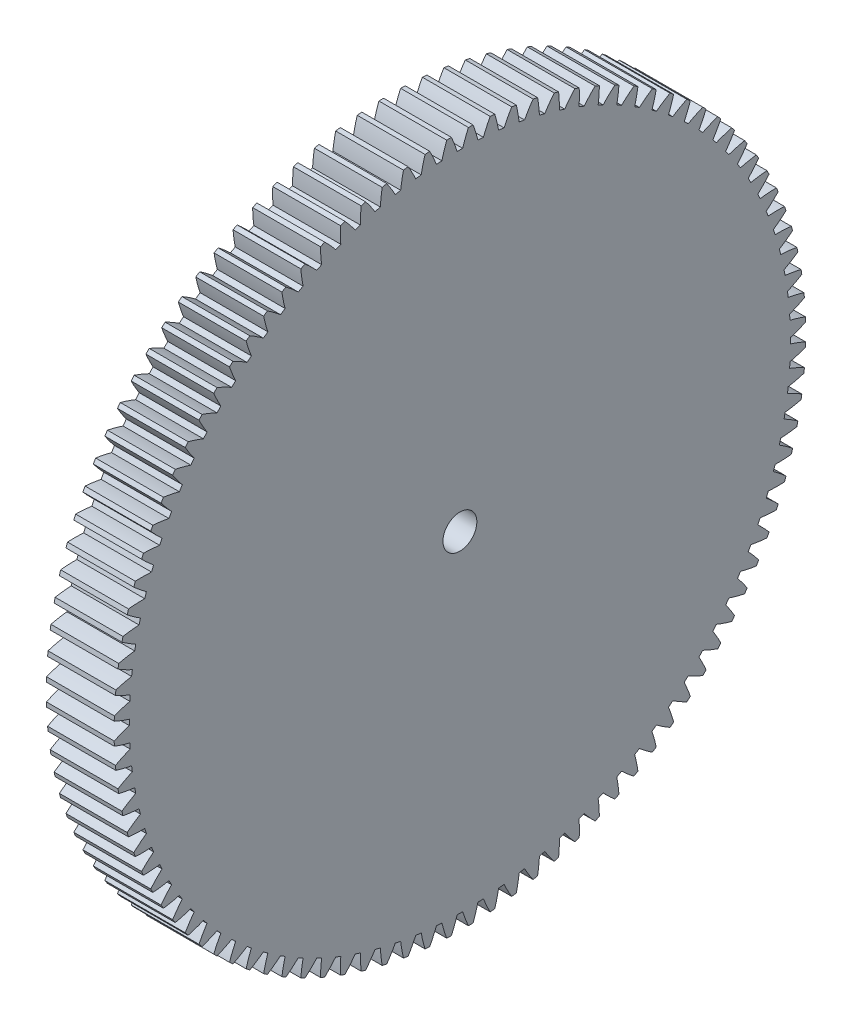
SolidWorks part; units mm, degrees
ref_plane "Plane1" through (0, 0, 0) normal (0, 0, 1) x (1, 0, 0)
ref_plane "Plane2" through (0, 0, 0) normal (0, 1, 0) x (1, 0, 0)
ref_plane "Plane3" through (0, 0, 0) normal (1, 0, 0) x (0, 0, -1)
sketch "HoldingSke" plane through (0, 0, 0) normal (0, 1, 0) x (1, 0, 0)
  line L0 (0, 0) -> (-0.0868, -0.4924)
  line L1 (-15, 0) -> (100, 0) construction
  line L2 (0, 0) -> (-2.1039, 2.3779)
  line L3 (0, 0) -> (-11.863, 4.5341)
  line L4 (0, 0) -> (-1.4996, 8.5048)
  line L5 (0, 0) -> (-46.8476, -17.4728)
  line L6 (0, 0) -> (-16.5793, -11.1861)
  line L7 (-2.1039, 2.3779) -> (8.6586, 51.2059)
  line L8 (-76.2, 54.61) -> (-74.4, 54.61)
  line L9 (-71.009, 38.7566) -> (-53.1078, 45.2721)
  line L10 (-76.2, 71.12) -> (104.1128, 71.12)
  line L11 (0, 0) -> (-20, 0)
  line L12 (-76.2, 101.6) -> (-76.133, 101.6)
  line L13 (24.9733, 27.94) -> (52.9518, 28.4284)
  line L14 (24.9733, 27.94) -> (24.9743, 27.94)
  line L15 (24.9733, 27.94) -> (100.4006, 29.5858)
  line L16 (-63.627, -2) -> (-12.827, -2)
  circle A0 centre (0, 0) radius 5
  circle A1 centre (0, 0) radius 37.5
  circle A2 centre (0, 0) radius 37.5
  circle A3 centre (0, 0) radius 5
  dimension "MHD" = 75
  dimension "Hub_dia" = 75
  dimension "Bore" = 10
  dimension "MBD" = 10
  dimension "Num_teeth" = 100
  dimension "Pitch" = 0.5
  dimension "Overall_len" = 50
  dimension "Show_teeth" = 100
  dimension "Thickness" = 20
  dimension "OAL" = 50.0001
  dimension "T_dim" = 1.8
  dimension "Ap" = 20
  dimension "H" = 19.05
  dimension "Pitch_radius" = 180.3128
  dimension "Width" = 20
  dimension "Backlash" = 0.067
  dimension "Addendum_fac" = 1
  dimension "Dedendum_fac" = 1.25
  dimension "Clearance_fac" = 0.25
  dimension "Dedendum_add" = 0.001
  dimension "Module" = 2
sketch "BasProSke" plane through (0, 0, 0) normal (0, 1, 0) x (1, 0, 0)
  line L0 (-10, 0) -> (60, 0) construction
  line L1 (0, 0) -> (0, 102)
  line L2 (0, 0) -> (20, 0)
  line L3 (20, 0) -> (20, 102)
  line L4 (20, 102) -> (0, 102)
  dimension "Thickness" = 20
  dimension "Diameter" = 204
revolve "Base-Revolve" add sketch "BasProSke" angle 360 about L0
sketch "TooCutSke" plane through (0, 0, 0) normal (1, 0, 0) x (0, 0, -1)
  line L1 (0, 0) -> (0, 107) construction
  line L2 (0, 0) -> (-1.688, 99.9858) construction
  line L3 (0, 0) -> (-6.2815, 199.8802) construction
  line L4 (-1.688, 99.9858) -> (-3.1407, 99.9401) construction
  arc A0 (0.8143, 97.4956) -> (-0.8143, 97.4956) centre (0, 0) ccw
  arc A1 (2.5315, 101.994) -> (-2.5315, 101.994) centre (0, 0) ccw
  circle A2 centre (0, 0) radius 100 construction
  circle A3 centre (0, 0) radius 93.9693 construction
  arc A4 (-0.8143, 97.4956) -> (-2.5315, 101.994) centre (-38.975, 85.5054) ccw
  arc A5 (2.5315, 101.994) -> (0.8143, 97.4956) centre (38.975, 85.5054) ccw
  dimension "Root_dia" = 194.998
  dimension "Overcut_dia" = 204.0508
  dimension "Pitch_dia" = 200
  dimension "Base_dia" = 187.9385
  dimension "Flank_rad" = 40
  dimension "Half_ang" = 1.8
  dimension "Half_CT" = 1.4535
extrude "ToothCut" cut sketch "TooCutSke" along normal through all
fillet "Breaks" [suppressed] radius 0.04
fillet "RootFillets" [suppressed] radius 0.501
pattern_circular "TeethCuts" count 100 every 3.6 about axis through (-10, 0, 0) along (1, 0, 0) of "ToothCut", "RootFillets", "Breaks"
sketch "HubNeaOneSke" plane through (0, 0, 0) normal (-1, 0, 0) x (0, 0, 1)
  circle A0 centre (0, 0) radius 37.5
  dimension "Diameter" = 75
extrude "HubNearOne" [suppressed] add sketch "HubNeaOneSke" along normal blind 30.0001
sketch "HubNeaBotSke" plane through (0, 0, 0) normal (-1, 0, 0) x (0, 0, 1)
  circle A0 centre (0, 0) radius 37.5
  dimension "Diameter" = 75
extrude "HubNearBoth" [suppressed] add sketch "HubNeaBotSke" along normal blind 15
ref_plane "FarPln" through (20, 0, 0) normal (1, 0, 0) x (0, 0, -1)
sketch "HubFarSke" plane through (20, 0, 0) normal (1, 0, 0) x (0, 0, -1)
  circle A0 centre (0, 0) radius 37.5
  dimension "Diameter" = 75
extrude "HubFar" [suppressed] add sketch "HubFarSke" along normal blind 15
sketch "BorSke" plane through (0, 0, 0) normal (1, 0, 0) x (0, 0, -1)
  circle A0 centre (0, 0) radius 5
  dimension "Diameter" = 10
extrude "Bore" cut sketch "BorSke" along normal mid plane 100.0001
sketch "KeySke" plane through (0, 0, 0) normal (1, 0, 0) x (0, 0, -1)
  line L0 (-2, 0) -> (-2, 6.8)
  line L1 (-2, 6.8) -> (2, 6.8)
  line L2 (2, 6.8) -> (2, 0)
  line L3 (0, 0) -> (0, 34) construction
  line L4 (-2, 0) -> (2, 0)
  dimension "Offset" = 6.8
  dimension "Width" = 4
extrude "Keyway" [suppressed] cut sketch "KeySke" along normal mid plane 100.0001
pattern_circular "Keyway2" [suppressed] count 2 every 90 about axis through (-10, 0, 0) along (1, 0, 0)
equation "' \"Module@HoldingSke\" = 6.35"
equation "' \"Num_teeth@HoldingSke\" = 12"
equation "' \"Ap@HoldingSke\" =  20"
equation "' \"Ap@HoldingSke\" = 20"
equation "' \"Width@HoldingSke\" = 0.5 * 25.4"
equation "' \"Hub_dia@HoldingSke\"= 1 * 25.4"
equation "' \"Hub_dia@HoldingSke\" = 1 * 25.4"
equation "' \"Overall_len@HoldingSke\" = 1.0 * 25.4"
equation "' \"Bore@HoldingSke\" = 0.75 * 25.4"
equation "' \"T_dim@HoldingSke\" = 0.1 * 25.4"
equation "' \"Width@KeySke\" = 0.25 * 25.4"
equation "' \"Show_teeth@HoldingSke\" = 13"
equation "' \"Backlash@HoldingSke\" = 0.009 * 25.4"
equation "' \"Addendum_fac@HoldingSke\" = 1.0"
equation "' \"Dedendum_fac@HoldingSke\" = 1.25"
equation "' \"Dedendum_add@HoldingSke\" = 0.00005 * 25.4"
equation "' \"Clearance_fac@HoldingSke\" = 0.25"
equation "\"Pitch@HoldingSke\" = 1 / \"Module@HoldingSke\""
equation "\"Overcut_dia@TooCutSke\" = (\"Num_teeth@HoldingSke\" + 2 * \"Addendum_fac@HoldingSke\") / \"Pitch@HoldingSke\" + 0.002 * 25.4"
equation "\"Pitch_dia@TooCutSke\" = \"Num_teeth@HoldingSke\" / \"Pitch@HoldingSke\""
equation "\"Base_dia@TooCutSke\" = \"Num_teeth@HoldingSke\" / \"Pitch@HoldingSke\" * cos((\"Ap@HoldingSke\"  * 3.14159265 / 180))"
equation "\"Root_dia@TooCutSke\" = (\"Num_teeth@HoldingSke\" + 2) / \"Pitch@HoldingSke\" - 2 * (\"Addendum_fac@HoldingSke\" + \"Dedendum_fac@HoldingSke\") / \"Pitch@HoldingSke\" - \"Dedendum_add@HoldingSke\" * 2"
equation "\"Half_ang@TooCutSke\" = 180 / \"Num_teeth@HoldingSke\""
equation "\"Half_CT@TooCutSke\" = \"Num_teeth@HoldingSke\" / \"Pitch@HoldingSke\" * sin((3.14159265 / 2 / \"Num_teeth@HoldingSke\")) / 2 - 7 * \"Backlash@HoldingSke\" / 4"
equation "\"Flank_rad@TooCutSke\" = \"Num_teeth@HoldingSke\" / \"Pitch@HoldingSke\" / 5"
equation "\"Radius@RootFillets\" = \"Clearance_fac@HoldingSke\" / \"Pitch@HoldingSke\" + \"Dedendum_add@HoldingSke\""
equation "\"Break_rad@Breaks\" = 0.02 / \"Pitch@HoldingSke\""
equation "\"Thickness@HoldingSke\" = \"Width@HoldingSke\""
equation "\"OAL@HoldingSke\" = \"Thickness@HoldingSke\""
equation "\"MHD@HoldingSke\" = (\"Num_teeth@HoldingSke\" + 2) / \"Pitch@HoldingSke\" - 2 * (\"Addendum_fac@HoldingSke\" + \"Dedendum_fac@HoldingSke\")  / \"Pitch@HoldingSke\" - \"Dedendum_add@HoldingSke\" * 2"
equation "\"MBD@HoldingSke\" = (\"Num_teeth@HoldingSke\" + 2) / \"Pitch@HoldingSke\" - 2 * (\"Addendum_fac@HoldingSke\" + \"Dedendum_fac@HoldingSke\")  / \"Pitch@HoldingSke\" - \"Dedendum_add@HoldingSke\" * 2 - 0.002 * 25.4"
equation "\"MHD@HoldingSke\" = ((sgn( \"MHD@HoldingSke\" - \"Hub_dia@HoldingSke\" )-1)*( \"MHD@HoldingSke\" - \"Hub_dia@HoldingSke\" ))/-2+ \"Hub_dia@HoldingSke\""
equation "\"MBD@HoldingSke\" = ((sgn( \"MBD@HoldingSke\" - \"Bore@HoldingSke\" )-1)*( \"MBD@HoldingSke\" - \"Bore@HoldingSke\" ))/-2+ \"Bore@HoldingSke\""
equation "\"OAL@HoldingSke\" = ((sgn( \"OAL@HoldingSke\" - \"Overall_len@HoldingSke\" )+1)*( \"OAL@HoldingSke\" - \"Overall_len@HoldingSke\" ))/2 + \"Overall_len@HoldingSke\" + 0.000002 * 25.4"
equation "\"Num_teeth@TeethCuts\" = int( \"Show_teeth@HoldingSke\" ) + 1"
equation "\"Num_teeth@TeethCuts\" = ((sgn( \"Num_teeth@TeethCuts\" - \"Num_teeth@HoldingSke\" )-1)*( \"Num_teeth@TeethCuts\" - \"Num_teeth@HoldingSke\" ))/-2+ \"Num_teeth@HoldingSke\""
equation "\"Num_teeth@TeethCuts\" = ((sgn( \"Num_teeth@TeethCuts\" - 2.0)+1)*( \"Num_teeth@TeethCuts\" - 2.0))/2 +2.0"
equation "\"Angle@TeethCuts\" = 360.0 / \"Num_teeth@HoldingSke\""
equation "\"Diameter@BasProSke\" = (\"Num_teeth@HoldingSke\" + 2 * \"Addendum_fac@HoldingSke\") / \"Pitch@HoldingSke\""
equation "\"Thickness@BasProSke\"  = \"Thickness@HoldingSke\""
equation "' \"Fillet_rad@BasProSke\" =  \"Thickness@HoldingSke\" * 0.05"
equation "' \"Fillet_rad@BasProSke\" = \"Thickness@HoldingSke\" * 0.05"
equation "\"MHD@HoldingSke\" = ((sgn( \"MHD@HoldingSke\" - \"Root_dia@TooCutSke\" )-1)*( \"MHD@HoldingSke\" - \"Root_dia@TooCutSke\" ))/-2+ \"Root_dia@TooCutSke\""
equation "\"Diameter@HubNeaOneSke\" = \"MHD@HoldingSke\""
equation "\"Length@HubNearOne\" = \"OAL@HoldingSke\" - \"Thickness@BasProSke\""
equation "\"Diameter@HubNeaBotSke\" = \"MHD@HoldingSke\""
equation "\"Length@HubNearBoth\" = ( \"OAL@HoldingSke\" - \"Thickness@BasProSke\" ) / 2.0"
equation "\"Thickness@FarPln\" = \"Thickness@BasProSke\""
equation "\"Diameter@HubFarSke\" = \"MHD@HoldingSke\""
equation "\"Length@HubFar\" = ( \"OAL@HoldingSke\" - \"Thickness@BasProSke\" ) / 2.0"
equation "\"Diameter@BorSke\" = \"MBD@HoldingSke\""
equation "\"D1@Bore\" = \"OAL@HoldingSke\" * 2.0"
equation "\"D1@Keyway\" = \"OAL@HoldingSke\" * 2.0"
equation "\"Offset@KeySke\" = \"T_dim@HoldingSke\" + \"MBD@HoldingSke\" / 2.0"
